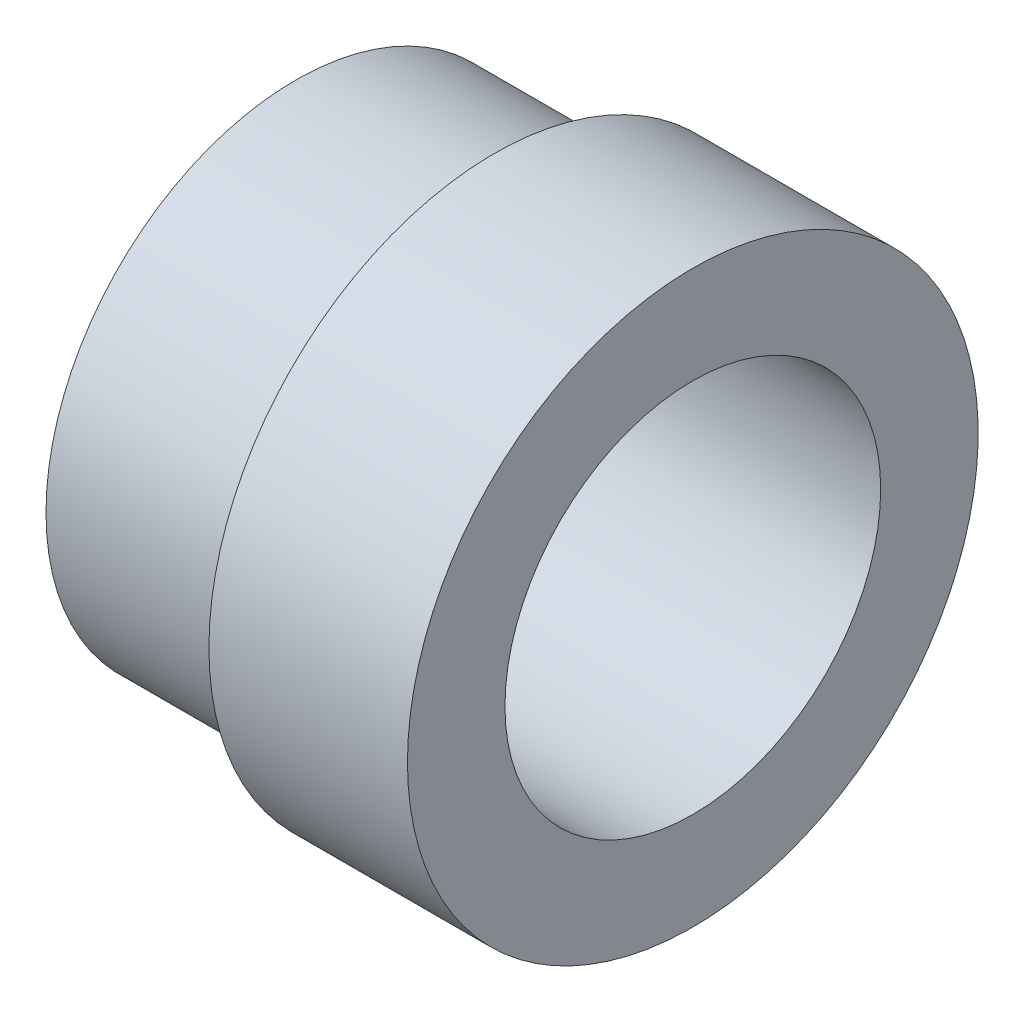
SolidWorks part; units mm, degrees
material "AISI 1020 Сталь, холоднокатаная"
ref_plane "Спереди" through (0, 0, 0) normal (0, 0, 1) x (1, 0, 0)
ref_plane "Сверху" through (0, 0, 0) normal (0, 1, 0) x (1, 0, 0)
ref_plane "Справа" through (0, 0, 0) normal (1, 0, 0) x (0, 0, -1)
sketch "Эскиз1" plane through (0, 0, 0) normal (0, 0, 1) x (1, 0, 0)
  line L0 (-98.05, -98) -> (-89.7, -98)
  line L1 (-89.7, -98) -> (-89.7, -102.1)
  line L2 (-89.7, -102.1) -> (-106.4, -102.1)
  line L3 (-106.4, -102.1) -> (-106.4, -99.5)
  line L4 (-106.4, -99.5) -> (-98.05, -99.5)
  line L5 (-98.05, -99.5) -> (-98.05, -98)
  line L6 (-89.5, -107.9961) -> (-89.5, -54.6737) construction
  line L7 (-98.05, -99.5) -> (-101.05, -99.5) construction
  line L8 (-98.05, -55) -> (-98.05, -162.2857) construction
  line L9 (-81.5, -102.1) -> (-89.5, -102.1) construction
  line L10 (-106.7519, -110) -> (-93.8138, -110) construction
  line L12 (-98.05, -110) -> (-101.05, -110) construction
  dimension "D1" = 0.2
  dimension "D2" = 1.5
revolve "Повернуть1" add sketch "Эскиз1" angle 360 about L10
